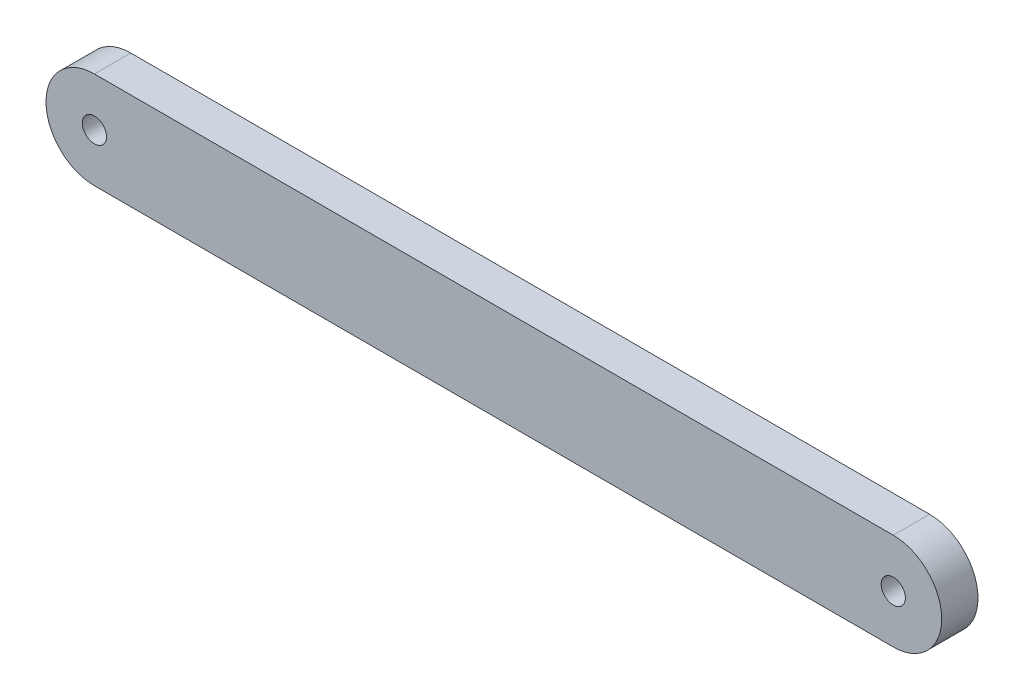
SolidWorks part; units mm, degrees
ref_plane "Plan de face" through (0, 0, 0) normal (0, 0, 1) x (1, 0, 0)
ref_plane "Plan de dessus" through (0, 0, 0) normal (0, 1, 0) x (1, 0, 0)
ref_plane "Plan de droite" through (0, 0, 0) normal (1, 0, 0) x (0, 0, -1)
sketch "Esquisse1" plane through (0, 0, 0) normal (0, 0, 1) x (1, 0, 0)
  line L0 (4, 8) -> (4, 0) construction
  line L1 (0, 0) -> (74, 0) construction
  line L2 (0, 0) -> (0, 8) construction
  line L3 (0, 8) -> (74, 8) construction
  line L4 (74, 0) -> (74, 8) construction
  line L5 (70, 8) -> (70, 0) construction
  line L6 (70, 8) -> (4, 8)
  line L7 (4, 0) -> (70, 0)
  arc A0 (4, 0) -> (4, 8) centre (4, 4) cw
  arc A1 (70, 8) -> (70, 0) centre (70, 4) cw
  circle A2 centre (4, 4) radius 1
  circle A3 centre (70, 4) radius 1
  dimension "D2" = 2
  dimension "D1" = 8
  dimension "D3" = 74
extrude "Boss.-Extru.1" add sketch "Esquisse1" along normal blind 3
